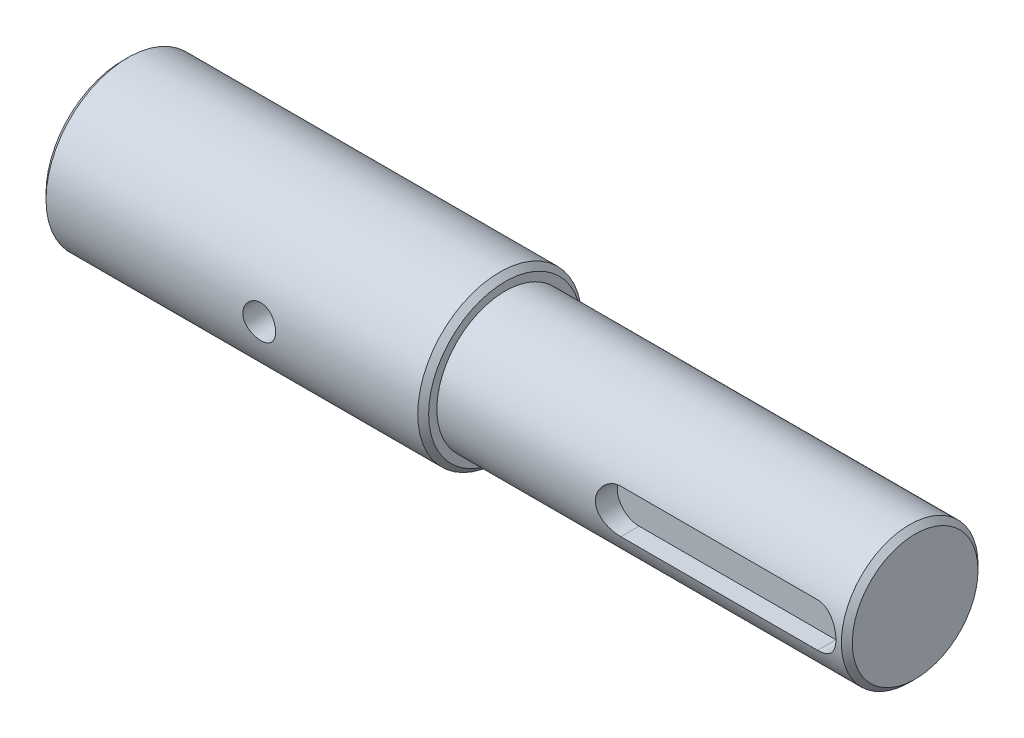
SolidWorks part; units mm, degrees
material "AISI 1045 钢，冷拔"
ref_plane "前视基准面" through (0, 0, 0) normal (0, 0, 1) x (1, 0, 0)
ref_plane "上视基准面" through (0, 0, 0) normal (0, 1, 0) x (1, 0, 0)
ref_plane "右视基准面" through (0, 0, 0) normal (1, 0, 0) x (0, 0, -1)
sketch "草图1" plane through (0, 0, 0) normal (1, 0, 0) x (0, 0, -1)
  circle A0 centre (0, 0) radius 12.5
  dimension "D1" = 25
extrude "凸台-拉伸1" add sketch "草图1" along normal blind 75
sketch "草图2" plane through (0, 0, 0) normal (-1, 0, 0) x (0, 0, 1)
  circle A0 centre (0, 0) radius 15
  dimension "D1" = 30
extrude "凸台-拉伸2" add sketch "草图2" along normal blind 70
chamfer "倒角1" distance 1 angle 45 3 edges at (75, 0, -12.5) (0, 0, 15) (-70, 0, 15)
ref_plane "基准面1" through (0, 0, 12.5) normal (0, 0, 1) x (1, 0, 0)
sketch "草图3" plane through (0, 0, 12.5) normal (0, 0, 1) x (1, 0, 0)
  line L0 (0, 0) -> (75, 0) construction
  line L1 (75, -11.5) -> (75, 11.5) construction
  line L4 (33, 4) -> (69, 4)
  line L7 (33, -4) -> (69, -4)
  arc A0 (69, -4) -> (69, 4) centre (69, 0) ccw
  arc A1 (33, 4) -> (33, -4) centre (33, 0) ccw
  point P5 (0, 4)
  point P6 (118, 4)
  point P7 (0, -4)
  point P8 (118, -4)
  dimension "D3" = 36
  dimension "D1" = 4
  dimension "D2" = 4
  dimension "D4" = 8
  dimension "D6" = 6
extrude "切除-拉伸1" cut sketch "草图3" against normal blind 4
sketch "草图4" plane through (0, 0, 0) normal (0, 0, 1) x (1, 0, 0)
  line L0 (0, 0) -> (-70, 0) construction
  line L1 (0, -14) -> (0, 14) construction
  line L2 (-70, 14) -> (-70, -14) construction
  circle A0 centre (-30, 0) radius 3
  dimension "D1" = 40
  dimension "D2" = 6
extrude "切除-拉伸2" cut sketch "草图4" against normal through all both and the other way through all
